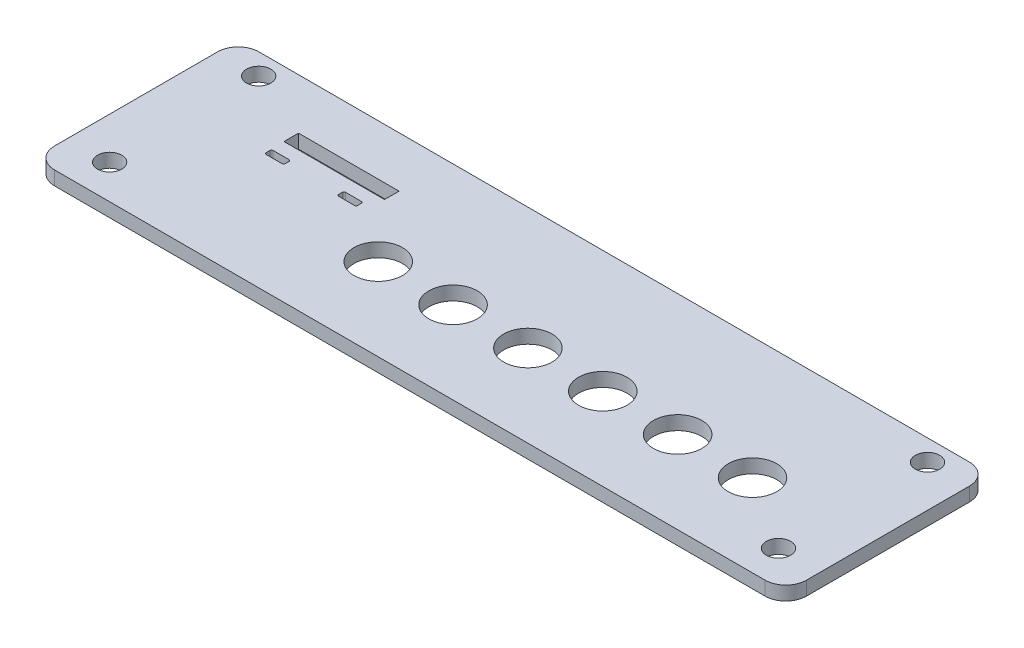
SolidWorks part; units mm, degrees
ref_plane "Front Plane" through (0, 0, 0) normal (0, 0, 1) x (1, 0, 0)
ref_plane "Top Plane" through (0, 0, 0) normal (0, 1, 0) x (1, 0, 0)
ref_plane "Right Plane" through (0, 0, 0) normal (1, 0, 0) x (0, 0, -1)
sketch "Sketch1" plane through (0, 0, 0) normal (0, 1, 0) x (1, 0, 0)
  line L1 (0, 0) -> (108.5, 0)
  line L2 (0, 0) -> (0, 29.5)
  line L3 (0, 29.5) -> (108.5, 29.5)
  line L4 (108.5, 0) -> (108.5, 29.5)
  dimension "D1" = 29.5
  dimension "D2" = 108.5
extrude "Boss-Extrude1" add sketch "Sketch1" along normal blind 2
sketch "Sketch2" plane through (0, 2, 0) normal (0, 1, 0) x (1, 0, 0)
  line L0 (54.25, 29.5) -> (54.25, 0) construction
  line L1 (108.5, 29.5) -> (0, 29.5) construction
  line L2 (0, 0) -> (108.5, 0) construction
  line L3 (0, 14.75) -> (108.5, 14.75) construction
  line L4 (0, 29.5) -> (0, 0) construction
  line L5 (108.5, 0) -> (108.5, 29.5) construction
  circle A0 centre (6, 26.45) radius 1.75
  circle A1 centre (6, 4.95) radius 1.75
  circle A2 centre (102.5, 4.95) radius 1.75
  circle A3 centre (102.5, 26.45) radius 1.75
  dimension "D1" = 3.5
  dimension "D4" = 3.5
  dimension "D2" = 48.25
  dimension "D3" = 11.7
  dimension "D5" = 9.8
  dimension "D6" = 48.25
extrude "Cut-Extrude1" cut sketch "Sketch2" against normal through all
fillet "Fillet1" radius 3 4 edges at (108.5, 1, 0) (108.5, 1, -29.5) (0, 1, 0) (0, 1, -29.5)
sketch "Sketch4" plane through (0, 2, 0) normal (0, 1, 0) x (1, 0, 0)
  line L2 (3, 0) -> (105.5, 0) construction
  line L4 (4, 7.7) -> (104.5, 7.7)
  line L5 (54.25, 29.5) -> (54.25, 0) construction
  line L6 (105.5, 29.5) -> (3, 29.5) construction
  line L7 (4, 7.7) -> (4, 9.7)
  line L8 (4, 9.7) -> (104.5, 9.7)
  line L9 (104.5, 9.7) -> (104.5, 7.7)
  dimension "D3" = 50.25
  dimension "D1" = 50.25
  dimension "D4" = 50.25
  dimension "D5" = 7.7
  dimension "D6" = 2
sketch "Sketch5" plane through (0, 2, 0) normal (0, 1, 0) x (1, 0, 0)
  line L0 (4, 9.7) -> (4, 18.2) construction
  line L1 (4, 18.2) -> (104.5, 18.2) construction
  line L2 (104.5, 18.2) -> (104.5, 9.7) construction
  line L3 (4, 20.2) -> (104.5, 20.2) construction
  line L4 (4, 18.2) -> (4, 20.2) construction
  line L5 (104.5, 18.2) -> (104.5, 20.2) construction
  line L6 (0, 26.5) -> (0, 3) construction
  line L7 (16, 20.1) -> (16, 18.2) construction
  line L8 (16, 20.1) -> (30.5, 20.1)
  line L9 (16, 20.1) -> (16, 22.2)
  line L10 (16, 22.2) -> (30.5, 22.2)
  line L11 (30.5, 20.1) -> (30.5, 22.2)
  line L13 (16.1, 18.2) -> (18.85, 18.2)
  line L14 (16.1, 18.2) -> (16.1, 17.2)
  line L15 (16.1, 17.2) -> (18.85, 17.2)
  line L16 (18.85, 18.2) -> (18.85, 17.2)
  line L17 (26.55, 18.2) -> (29.3, 18.2)
  line L18 (26.55, 18.2) -> (26.55, 17.2)
  line L19 (26.55, 17.2) -> (29.3, 17.2)
  line L20 (29.3, 18.2) -> (29.3, 17.2)
  line L27 (108.5, 3) -> (108.5, 26.5) construction
  circle A0 centre (91.8, 11.9) radius 3.5
  circle A1 centre (81, 11.9) radius 3.5
  circle A2 centre (70.2, 11.9) radius 3.5
  circle A3 centre (59.4, 11.9) radius 3.5
  circle A4 centre (48.6, 11.9) radius 3.5
  circle A5 centre (37.8, 11.9) radius 3.5
  point P24 (16, 21.15)
  point P38 (30.5, 21.15)
  dimension "D3" = 7
  dimension "D1" = 8.5
  dimension "D4" = 6
  dimension "D5" = 16.7
  dimension "D6" = 6.3
  dimension "D7" = 2.1
  dimension "D8" = 0.1
  dimension "D9" = 14.5
  dimension "D10" = 16
  dimension "D11" = 1
  dimension "D12" = 0.1
  dimension "D13" = 2.75
  dimension "D14" = 7.7
  dimension "D15" = 2.75
  dimension "D16" = 1.2
  dimension "D22" = 108.5
extrude "Cut-Extrude2" cut sketch "Sketch5" against normal through all
fillet "Fillet2" radius 0.2 8 edges at (26.55, 1, -18.2) (18.85, 1, -18.2) (29.3, 1, -18.2) (29.3, 1, -17.2) (18.85, 1, -17.2) (26.55, 1, -17.2) (16.1, 1, -17.2) (16.1, 1, -18.2)
